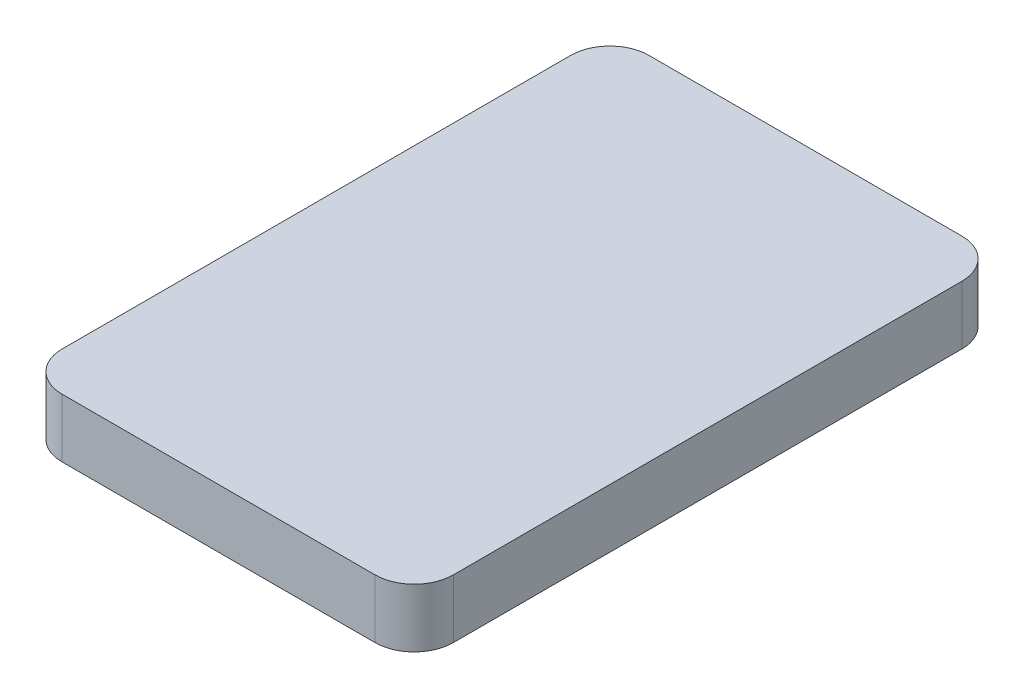
SolidWorks part; units mm, degrees
ref_plane "Front Plane" through (0, 0, 0) normal (0, 0, 1) x (1, 0, 0)
ref_plane "Top Plane" through (0, 0, 0) normal (0, 1, 0) x (1, 0, 0)
ref_plane "Right Plane" through (0, 0, 0) normal (1, 0, 0) x (0, 0, -1)
sketch "Sketch1" plane through (0, 0, 0) normal (0, 1, 0) x (1, 0, 0)
  line L1 (-8, 15) -> (8, 15)
  line L2 (-10, 13) -> (-10, -13)
  line L3 (-8, -15) -> (8, -15)
  line L4 (10, 13) -> (10, -13)
  line L5 (-10, 15) -> (10, -15) construction
  line L6 (-10, -15) -> (10, 15) construction
  arc A0 (-10, -13) -> (-8, -15) centre (-8, -13) ccw
  arc A1 (8, -15) -> (10, -13) centre (8, -13) ccw
  arc A2 (8, 15) -> (10, 13) centre (8, 13) cw
  arc A3 (-8, 15) -> (-10, 13) centre (-8, 13) ccw
  point P0 (0, 0)
  dimension "D3" = 2
  dimension "D1" = 30
  dimension "D2" = 20
extrude "Boss-Extrude1" add sketch "Sketch1" along normal blind 3
